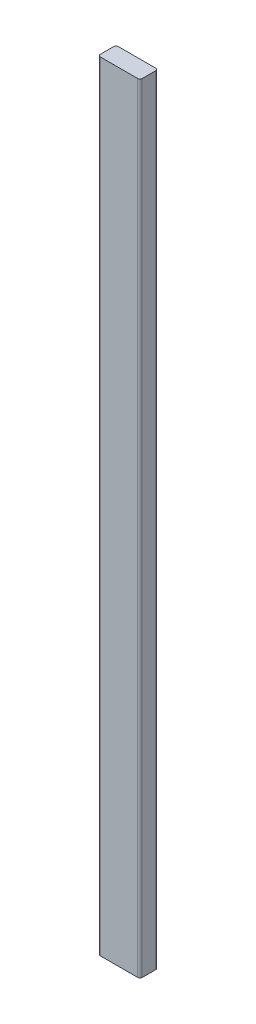
SolidWorks part; units mm, degrees
material "Pine"
ref_plane "Front Plane" through (0, 0, 0) normal (0, 0, 1) x (1, 0, 0)
ref_plane "Top Plane" through (0, 0, 0) normal (0, 1, 0) x (1, 0, 0)
ref_plane "Right Plane" through (0, 0, 0) normal (1, 0, 0) x (0, 0, -1)
sketch "Sketch1" plane through (0, 0, 0) normal (0, 0, 1) x (1, 0, 0)
  line L0 (-781.7306, 0) -> (-204.9322, 0) construction
  line L1 (-547.8322, 1651) -> (-458.9322, 1651)
  line L2 (-547.8322, 1651) -> (-547.8322, 0)
  line L3 (-547.8322, 0) -> (-458.9322, 0)
  line L4 (-458.9322, 1651) -> (-458.9322, 0)
  line L5 (-458.9322, 88.9) -> (-458.9322, 304.7381) construction
extrude "Boss-Extrude1" add sketch "Sketch1" against normal up to surface (38.1 mm away)
fillet "Fillet1" radius 4.7625 4 edges at (-547.8322, 825.5, -38.1) (-547.8322, 825.5, 0) (-458.9322, 825.5, -38.1) (-458.9322, 825.5, 0)
ref_plane "Plane1" through (-503.3822, 0, 0) normal (1, 0, 0) x (0, 0, -1)
